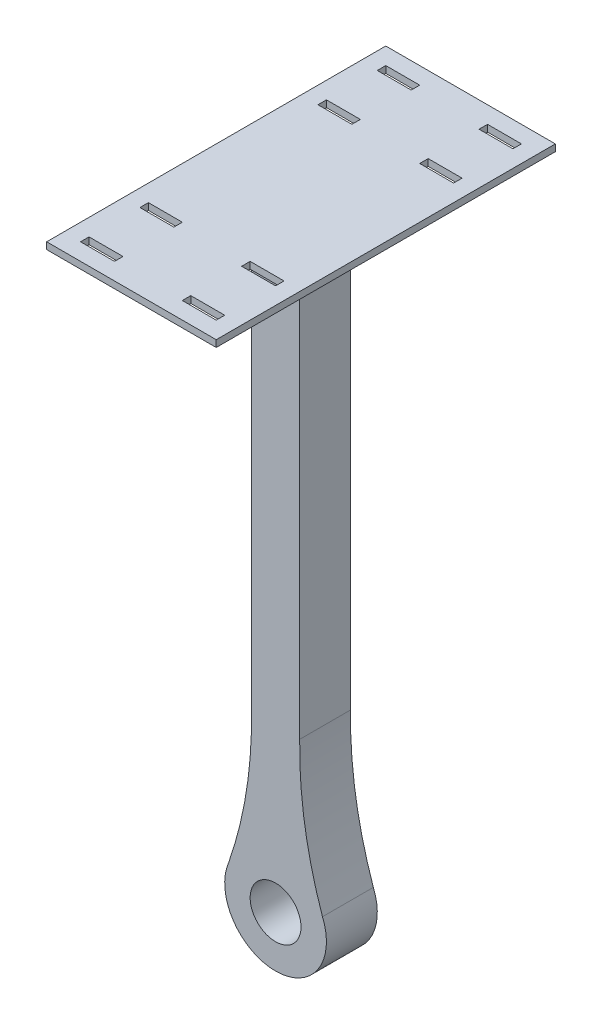
SolidWorks part; units mm, degrees
material "1023 Carbon Steel Sheet (SS)"
ref_plane "Front Plane" through (0, 0, 0) normal (0, 0, 1) x (1, 0, 0)
ref_plane "Top Plane" through (0, 0, 0) normal (0, 1, 0) x (1, 0, 0)
ref_plane "Right Plane" through (0, 0, 0) normal (1, 0, 0) x (0, 0, -1)
sketch "Sketch1" plane through (0, 0, 0) normal (0, 0, 1) x (1, 0, 0)
  circle A0 centre (0, 0) radius 15
  circle A1 centre (0, 0) radius 30
  dimension "D1" = 30
  dimension "D2" = 60
extrude "Boss-Extrude1" add sketch "Sketch1" along normal mid plane 30
sketch "Sketch2" plane through (0, 0, 15) normal (0, 0, 1) x (1, 0, 0)
  line L0 (0, 0) -> (0, 151.3005) construction
  line L1 (14.2415, 95.5022) -> (14.2415, 360)
  line L2 (-14.2415, 95.5022) -> (-14.2415, 360)
  line L3 (-14.2415, 360) -> (14.2415, 360)
  circle A2 centre (0, 0) radius 30 construction
  arc A3 (27.6704, 11.5909) -> (-27.6704, 11.5909) centre (0, 0) ccw
  spline S0 degree 2 poles (27.6704, 11.5909) (13.4956, 52.4694) (14.2415, 95.5022) knots 0 0 0 1 1 1
  spline S1 degree 2 poles (-27.6704, 11.5909) (-13.4956, 52.4694) (-14.2415, 95.5022) knots 0 0 0 1 1 1
  dimension "D1" = 360
extrude "Boss-Extrude2" add sketch "Sketch2" against normal blind 30
sketch "Sketch3" plane through (0, 360, 0) normal (0, 1, 0) x (1, 0, 0)
  line L0 (14.2415, 15) -> (14.2415, -15) construction
  line L1 (50, 100) -> (-50, 100)
  line L2 (50, 100) -> (50, -100)
  line L3 (50, -100) -> (-50, -100)
  line L4 (-50, 100) -> (-50, -100)
  line L5 (50, 100) -> (-50, -100) construction
  line L6 (50, -100) -> (-50, 100) construction
  point P0 (0, 0)
  point P5 (0, 100)
  point P9 (14.2415, 0)
  point P10 (50, 0)
  dimension "D1" = 100
  dimension "D2" = 200
extrude "Boss-Extrude3" add sketch "Sketch3" against normal blind 4
sketch "Sketch4" plane through (0, 356, 0) normal (0, -1, 0) x (1, 0, 0)
  line L0 (-50, -100) -> (-50, 100) construction
  line L5 (-50, 100) -> (50, 100) construction
  line L6 (50, 100) -> (50, -100) construction
  line L11 (-91.9395, 0) -> (99.4561, 0) construction
  line L12 (-20, -85) -> (-40, -90) construction
  line L13 (40, 90) -> (20, 90)
  line L14 (40, 90) -> (40, 85)
  line L15 (40, 85) -> (20, 85)
  line L16 (20, 90) -> (20, 85)
  line L17 (40, 90) -> (20, 85) construction
  line L18 (40, 85) -> (20, 90) construction
  line L19 (-20, 90) -> (-40, 90)
  line L20 (-20, 90) -> (-20, 85)
  line L21 (-20, 85) -> (-40, 85)
  line L22 (-40, 90) -> (-40, 85)
  line L23 (-20, 90) -> (-40, 85) construction
  line L24 (-20, 85) -> (-40, 90) construction
  line L25 (-20, -90) -> (-40, -85) construction
  line L26 (40, -85) -> (20, -90) construction
  line L27 (40, -90) -> (20, -85) construction
  line L28 (-40, -90) -> (-40, -85)
  line L29 (-20, -85) -> (-40, -85)
  line L30 (-20, -90) -> (-20, -85)
  line L31 (-20, -90) -> (-40, -90)
  line L32 (20, -90) -> (20, -85)
  line L33 (40, -85) -> (20, -85)
  line L34 (40, -90) -> (40, -85)
  line L35 (40, -90) -> (20, -90)
  line L36 (99.4561, -70) -> (-91.9395, -70) construction
  line L38 (99.4561, 70) -> (-91.9395, 70) construction
  line L39 (-20, 55) -> (-40, 50) construction
  line L40 (-20, 50) -> (-40, 55) construction
  line L41 (40, 55) -> (20, 50) construction
  line L42 (40, 50) -> (20, 55) construction
  line L43 (-40, 50) -> (-40, 55)
  line L44 (-20, 55) -> (-40, 55)
  line L45 (-20, 50) -> (-20, 55)
  line L46 (-20, 50) -> (-40, 50)
  line L47 (20, 50) -> (20, 55)
  line L48 (40, 55) -> (20, 55)
  line L49 (40, 50) -> (40, 55)
  line L50 (40, 50) -> (20, 50)
  line L51 (40, -50) -> (20, -55) construction
  line L52 (40, -55) -> (20, -50) construction
  line L53 (-20, -50) -> (-40, -55) construction
  line L54 (-20, -55) -> (-40, -50) construction
  line L55 (40, -50) -> (20, -50)
  line L56 (40, -50) -> (40, -55)
  line L57 (40, -55) -> (20, -55)
  line L58 (20, -50) -> (20, -55)
  line L59 (-20, -50) -> (-40, -50)
  line L60 (-20, -50) -> (-20, -55)
  line L61 (-20, -55) -> (-40, -55)
  line L62 (-40, -50) -> (-40, -55)
  point P10 (30, 87.5)
  point P15 (-30, 87.5)
  point P28 (-30, -87.5)
  point P29 (30, -87.5)
  point P41 (-30, 52.5)
  point P42 (30, 52.5)
  point P51 (30, -52.5)
  point P52 (-30, -52.5)
  dimension "D1" = 10
  dimension "D2" = 10
  dimension "D3" = 20
  dimension "D4" = 5
  dimension "D5" = 10
  dimension "D6" = 5
  dimension "D7" = 10
  dimension "D8" = 20
  dimension "D9" = 70
  dimension "D10" = 70
extrude "Cut-Extrude1" cut sketch "Sketch4" against normal blind 4
